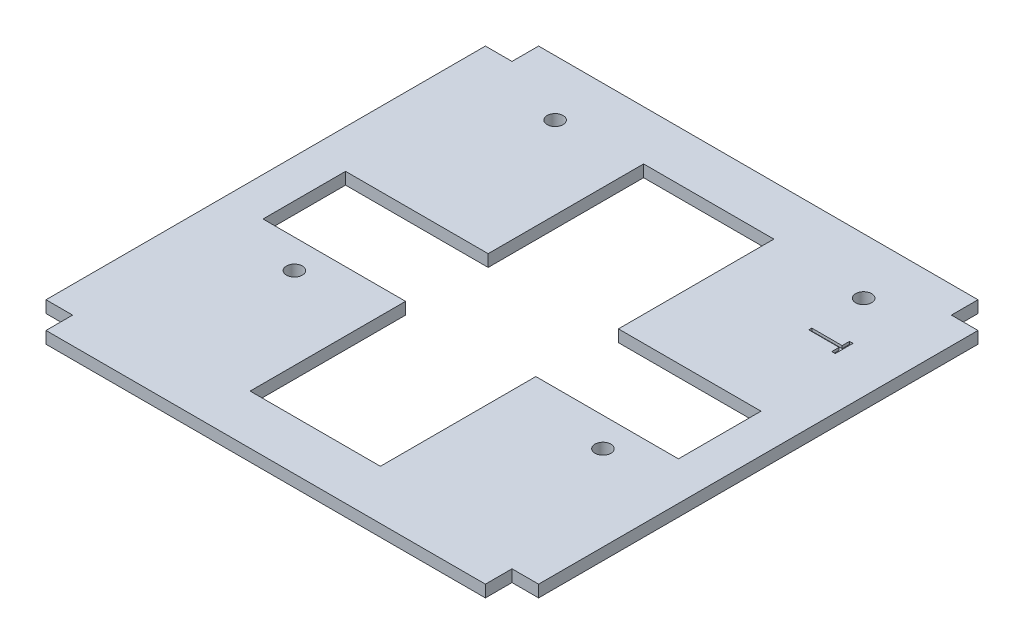
SolidWorks part; units mm, degrees
ref_plane "Front" through (0, 0, 0) normal (0, 0, 1) x (1, 0, 0)
ref_plane "Top" through (0, 0, 0) normal (0, 1, 0) x (1, 0, 0)
ref_plane "Right" through (0, 0, 0) normal (1, 0, 0) x (0, 0, -1)
sketch "Sketch2" plane through (0, 0, 0) normal (0, 1, 0) x (1, 0, 0)
  line L1 (-46.3, 41.3) -> (46.3, 41.3)
  line L2 (-46.3, 41.3) -> (-46.3, -41.3)
  line L3 (-46.3, -41.3) -> (46.3, -41.3)
  line L4 (46.3, 41.3) -> (46.3, -41.3)
  line L5 (-46.3, 41.3) -> (46.3, -41.3) construction
  line L6 (-46.3, -41.3) -> (46.3, 41.3) construction
  line L7 (-41.3, 46.3) -> (41.3, 46.3)
  line L8 (-41.3, 46.3) -> (-41.3, -46.3)
  line L9 (-41.3, -46.3) -> (41.3, -46.3)
  line L10 (41.3, 46.3) -> (41.3, -46.3)
  line L11 (-41.3, 46.3) -> (41.3, -46.3) construction
  line L12 (-41.3, -46.3) -> (41.3, 46.3) construction
  point P0 (0, 0)
  point P6 (0, 0)
  dimension "D1" = 82.6
  dimension "D2" = 92.6
  dimension "D3" = 92.6
  dimension "D4" = 82.6
extrude "Boss-Extrude1" add sketch "Sketch2" along normal blind 2.25 contours L8 L1 L2 L3 | L10 L1 L8 L3 | L10 L3 L8 L9 | L1 L10 L3 L4 | L10 L7 L8 L1
sketch "Sketch5" plane through (0, 2.25, 0) normal (0, 1, 0) x (1, 0, 0)
  line L1 (-27.7, 35.8) -> (30.3, 35.8) construction
  line L2 (-27.7, 35.8) -> (-27.7, -13.2) construction
  line L3 (-27.7, -13.2) -> (30.3, -13.2) construction
  line L4 (30.3, 35.8) -> (30.3, -13.2) construction
  line L5 (-27.7, 35.8) -> (30.3, -13.2) construction
  line L6 (-27.7, -13.2) -> (30.3, 35.8) construction
  line L7 (46.3, 41.3) -> (46.3, -41.3) construction
  line L8 (41.3, 41.3) -> (46.3, 41.3) construction
  circle A0 centre (-27.7, 35.8) radius 1.5
  circle A1 centre (30.3, 35.8) radius 1.5
  circle A2 centre (30.3, -13.2) radius 1.5
  circle A3 centre (-27.7, -13.2) radius 1.5
  point P0 (1.3, 11.3)
  dimension "D5" = 3
  dimension "D6" = 3
  dimension "D7" = 3
  dimension "D8" = 3
  dimension "D1" = 49
  dimension "D2" = 58
  dimension "D3" = 5.5
  dimension "D4" = 16
extrude "Cut-Extrude3" cut sketch "Sketch5" against normal blind 10
sketch "Sketch6" plane through (0, 2.25, 0) normal (0, 1, 0) x (1, 0, 0)
  line L1 (-12.2438, 36.9851) -> (12.2438, 36.9851)
  line L2 (-12.2438, 36.9851) -> (-12.2438, -36.9851)
  line L3 (-12.2438, -36.9851) -> (12.2438, -36.9851)
  line L4 (12.2438, 36.9851) -> (12.2438, -36.9851)
  line L5 (-12.2438, 36.9851) -> (12.2438, -36.9851) construction
  line L6 (-12.2438, -36.9851) -> (12.2438, 36.9851) construction
  line L7 (-39.0469, 7.7618) -> (39.0469, 7.7618)
  line L8 (-39.0469, 7.7618) -> (-39.0469, -7.7618)
  line L9 (-39.0469, -7.7618) -> (39.0469, -7.7618)
  line L10 (39.0469, 7.7618) -> (39.0469, -7.7618)
  line L11 (-39.0469, 7.7618) -> (39.0469, -7.7618) construction
  line L12 (-39.0469, -7.7618) -> (39.0469, 7.7618) construction
  point P0 (0, 0)
  point P6 (0, 0)
extrude "Cut-Extrude4" cut sketch "Sketch6" against normal blind 10 contours L2 L7 L4 L1 | L2 L9 L4 L7 | L10 L7 L4 L9 | L9 L2 L3 L4 | L8 L9 L2 L7
sketch "Sketch7" plane through (0, 2.25, 0) normal (0, 1, 0) x (1, 0, 0)
  line L0 (30.3, 37.3) -> (30.3, -11.7) construction
  circle A0 centre (30.3, 35.8) radius 1.5 construction
  circle A1 centre (30.3, -13.2) radius 1.5 construction
  text T0 "    T"
extrude "Cut-Extrude5" cut sketch "Sketch7" against normal blind 0.5
